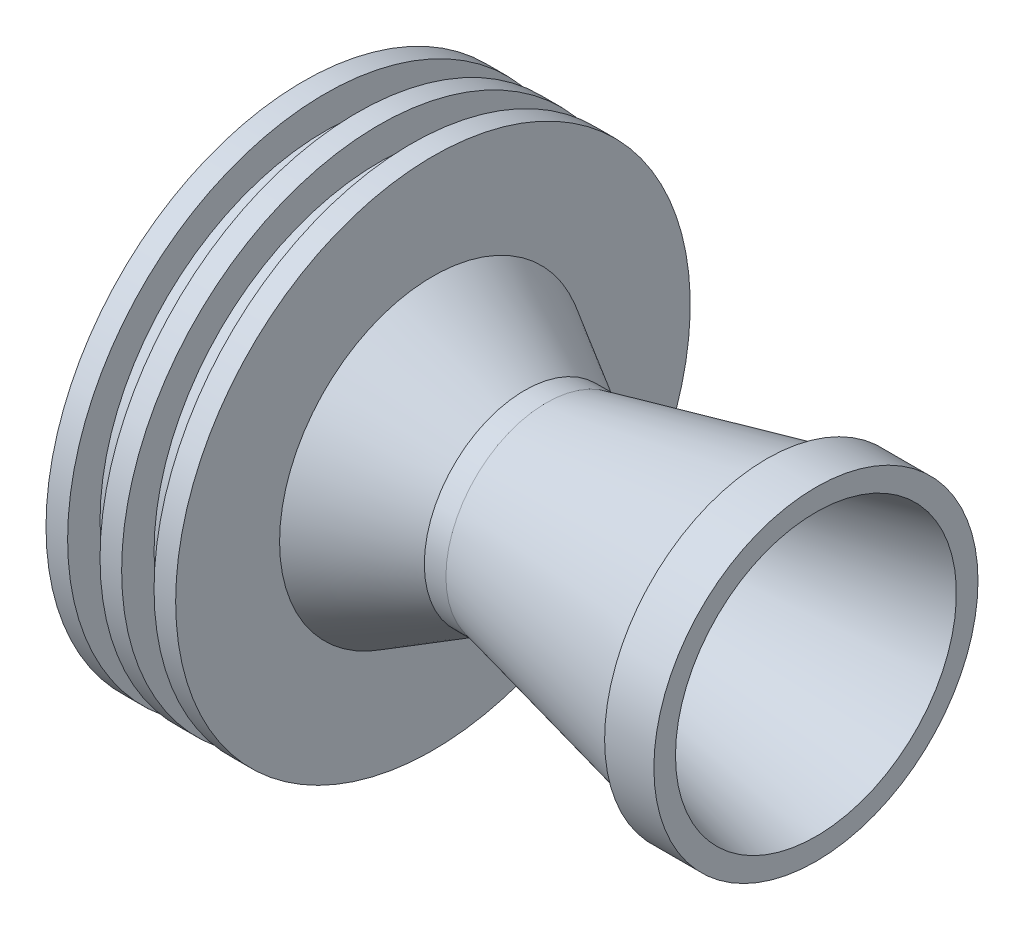
SolidWorks part; units mm, degrees
ref_plane "Plano frontal" through (0, 0, 0) normal (0, 0, 1) x (1, 0, 0)
ref_plane "Plano superior" through (0, 0, 0) normal (0, 1, 0) x (1, 0, 0)
ref_plane "Plano direito" through (0, 0, 0) normal (1, 0, 0) x (0, 0, -1)
sketch "Esboço2" plane through (0, 0, 0) normal (0, 0, 1) x (1, 0, 0)
  line L0 (-1000, 0) -> (49000, 0) construction
  line L1 (0, -1000) -> (0, 49000) construction
  line L50 (0, 23.8125) -> (2, 23.8125)
  line L51 (2, 23.8125) -> (2, 20.8125)
  line L52 (2, 20.8125) -> (5, 20.8125)
  line L53 (5, 20.8125) -> (5, 23.8125)
  line L54 (5, 23.8125) -> (7, 23.8125)
  line L55 (7, 23.8125) -> (7, 20.8125)
  line L56 (7, 20.8125) -> (10, 20.8125)
  line L57 (10, 20.8125) -> (10, 23.8125)
  line L58 (10, 23.8125) -> (12, 23.8125)
  line L59 (12, 23.8125) -> (12, 20.8125)
  line L61 (20.4919, 9.2909) -> (22.4919, 9.2909)
  line L62 (22.4919, 9.2909) -> (42.8894, 14)
  line L63 (42.8894, 14) -> (42.8894, 15)
  line L64 (42.8894, 15) -> (47.4487, 15)
  line L65 (47.4487, 15) -> (47.4487, 13)
  line L68 (20.4599, 7) -> (0, 18.8125)
  line L69 (0, 23.8125) -> (0, 20.8125)
  line L70 (0, 20.8125) -> (0, 18.8125)
  line L71 (12, 20.8125) -> (12, 14.1937)
  line L72 (12, 14.1937) -> (20.4919, 9.2909)
  line L73 (20.4599, 7) -> (21.4599, 7)
  line L74 (21.4599, 7) -> (47.4487, 13)
  dimension "45" = 30
  dimension "D1" = 3
  dimension "D3" = 2
  dimension "D4" = 3
  dimension "D5" = 2
  dimension "D6" = 23.8125
  dimension "D8" = 2
  dimension "D2" = 13
  dimension "D11" = 1
  dimension "D7" = 2
  dimension "D12" = 7
  dimension "D10" = 13
  dimension "2" = 2
  dimension "D9" = 1
  dimension "D13" = 2
revolve "Revolução1" add sketch "Esboço2" angle 360 about L0
equation "\"D6@Esboço2\"=25.4*(2-2*(1/16))/2"
